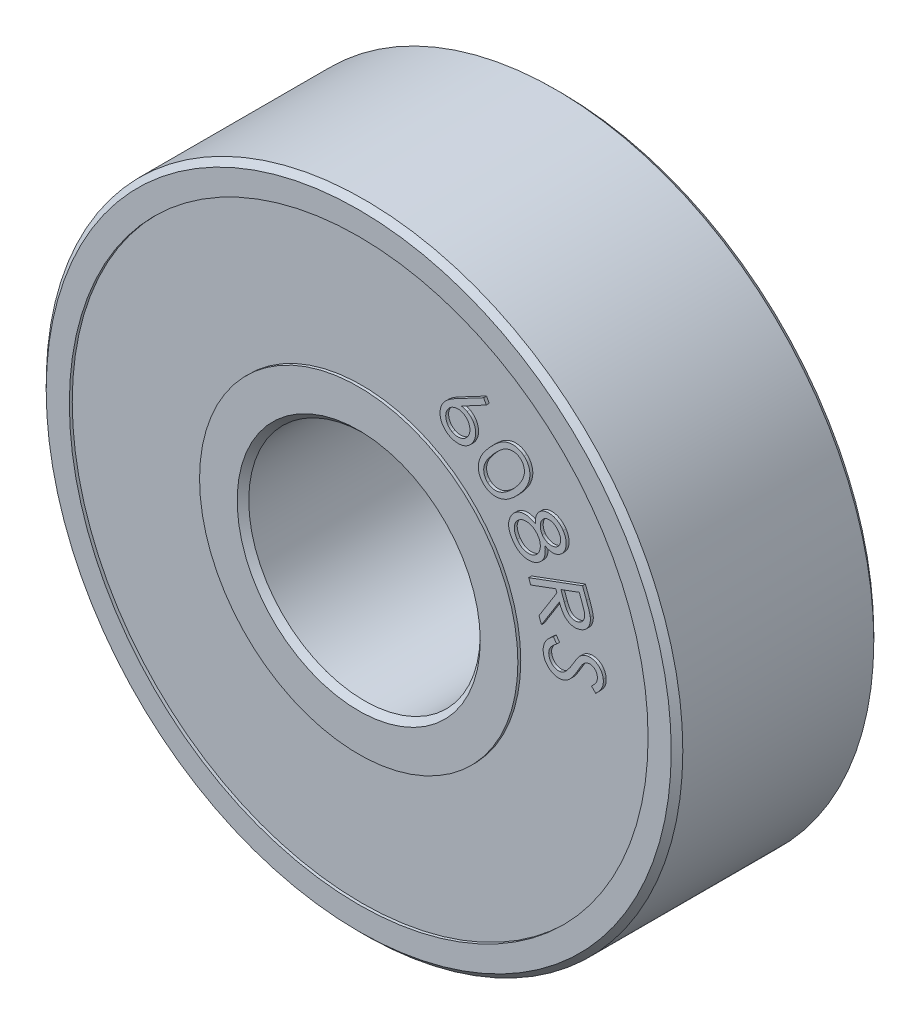
SolidWorks part; units mm, degrees
material "Stainless Steel (ferritic)"
ref_plane "Front Plane" through (0, 0, 0) normal (0, 0, 1) x (1, 0, 0)
ref_plane "Top Plane" through (0, 0, 0) normal (0, 1, 0) x (1, 0, 0)
ref_plane "Right Plane" through (0, 0, 0) normal (1, 0, 0) x (0, 0, -1)
sketch "Sketch1" plane through (0, 0, 0) normal (0, 0, 1) x (1, 0, 0)
  circle A0 centre (0, 0) radius 11
  circle A1 centre (0, 0) radius 4
extrude "Boss-Extrude1" add sketch "Sketch1" along normal blind 7
sketch "Sketch2" plane through (0, 0, 0) normal (0, 0, 1) x (1, 0, 0)
  circle A0 centre (0, 0) radius 5.5
  circle A1 centre (0, 0) radius 10
extrude "Cut-Extrude2" cut sketch "Sketch2" along normal blind 0.1
sketch "Sketch4" plane through (0, 0, 7) normal (0, 0, 1) x (1, 0, 0)
  circle A0 centre (0, 0) radius 5.5
  circle A1 centre (0, 0) radius 10
extrude "Cut-Extrude3" cut sketch "Sketch4" against normal blind 0.1
chamfer "Chamfer1" distance 0.2 angle 45 4 edges at (4, 0, 0) (11, 0, 0) (11, 0, 7) (4, 0, 7)
sketch "Sketch6" plane through (0, 0, 0) normal (0, 0, 1) x (1, 0, 0)
  circle A0 centre (0, 0) radius 6.5 construction
  text T0 "608RS" font "Century Gothic" height 2
extrude "Boss-Extrude2" add sketch "Sketch6" along normal blind 0.1
sketch "Sketch7" plane through (0, 0, 6.9) normal (0, 0, 1) x (1, 0, 0)
  circle A0 centre (0, 0) radius 6.5 construction
  text T0 "608RS" font "Century Gothic" height 2
extrude "Boss-Extrude3" add sketch "Sketch7" along normal blind 0.1
